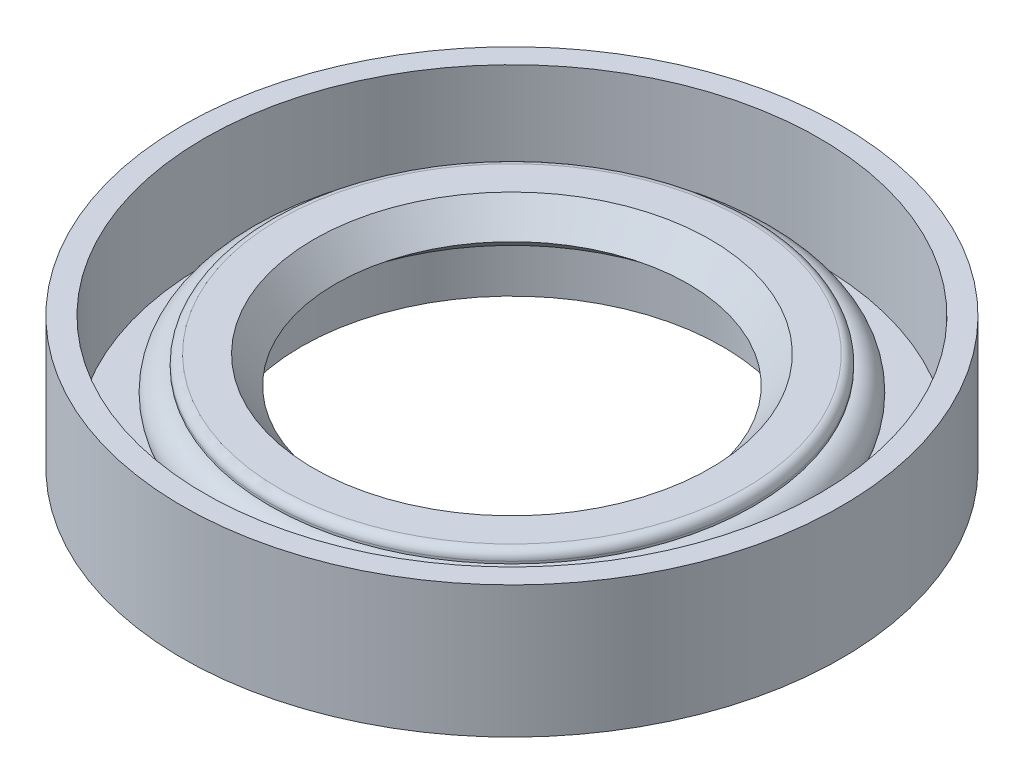
SolidWorks part; units mm, degrees
ref_plane "Front Plane" through (0, 0, 0) normal (0, 0, 1) x (1, 0, 0)
ref_plane "Top Plane" through (0, 0, 0) normal (0, 1, 0) x (1, 0, 0)
ref_plane "Right Plane" through (0, 0, 0) normal (1, 0, 0) x (0, 0, -1)
sketch "Sketch1" plane through (0, 0, 0) normal (0, 0, 1) x (1, 0, 0)
  line L0 (0, 14.8286) -> (0, -14.8286) construction
  line L2 (9.5857, -4.4143) -> (15, -4.4143)
  line L3 (15, -4.4143) -> (15, 1.5857)
  line L4 (15, 1.5857) -> (14, 1.5857)
  line L5 (14, 1.5857) -> (14, -3.4143)
  line L6 (14, -3.4143) -> (11, -3.4143)
  line L7 (11, -3.4143) -> (11, -2.4143)
  line L12 (11, -0.4143) -> (11, -0.3143)
  line L13 (10.6, 0.0857) -> (9.0245, 0.0857)
  line L14 (9.0245, 0.0857) -> (8.0245, -1.1643)
  line L15 (8.0245, -1.1643) -> (9.5857, -2.4143)
  line L16 (9.5857, -2.4143) -> (9.5857, -4.4143)
  arc A0 (11, -2.4143) -> (11, -0.4143) centre (11, -1.4143) ccw
  arc A1 (11, -0.3143) -> (10.6, 0.0857) centre (10.6, -0.3143) ccw
  point P4 (0, 0)
  point P19 (11, 0.0857)
  dimension "D5" = 1
  dimension "D6" = 2
  dimension "D8" = 1.6008
  dimension "D13" = 0.4
  dimension "D1" = 3
  dimension "D2" = 1
  dimension "D3" = 1
  dimension "D4" = 3
  dimension "D7" = 0.5
  dimension "D9" = 1
  dimension "D10" = 14
  dimension "D11" = 1
  dimension "D12" = 6
  dimension "D14" = 15
  dimension "D15" = 11
revolve "Revolve1" add sketch "Sketch1" angle 360 about L0
